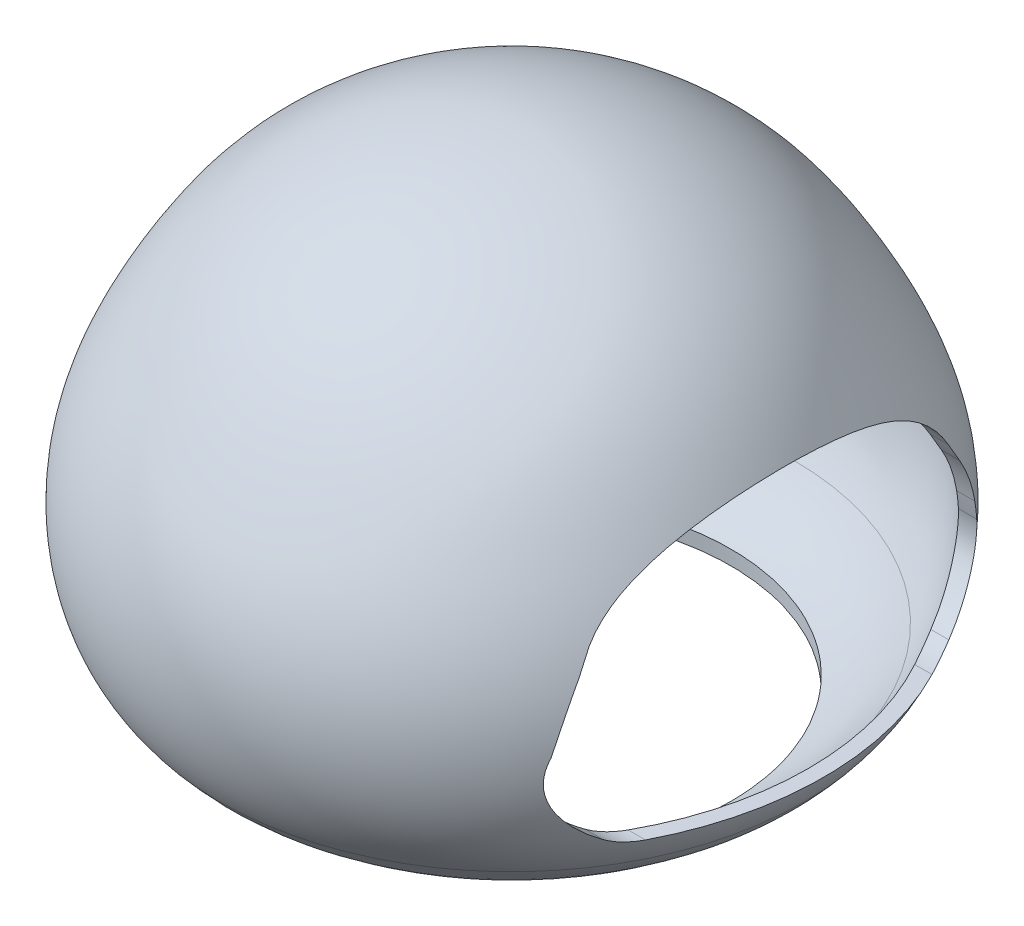
SolidWorks part; units mm, degrees
ref_plane "Front Plane" through (0, 0, 0) normal (0, 0, 1) x (1, 0, 0)
ref_plane "Top Plane" through (0, 0, 0) normal (0, 1, 0) x (1, 0, 0)
ref_plane "Right Plane" through (0, 0, 0) normal (1, 0, 0) x (0, 0, -1)
sketch "Sketch3" plane through (0, 0, 0) normal (0, 0, 1) x (1, 0, 0)
  line L0 (0.0245, 157.0849) -> (0.0245, 152.0849)
  line L1 (0.0245, -20.9434) -> (0.0245, -25.9434)
  line L2 (0.0245, 171.6103) -> (0.0245, -40.6784) construction
  spline S0 degree 3 poles (-103.1746, 0) (-78.8328, -30.0641) (-33.4587, -20.9434) (0.0245, -20.9434) knots 0 0 0 0 1 1 1 1
  spline S1 degree 3 poles (-103.1746, 0) (-114.7602, 14.5762) (-119.8367, 49.2728) (-101.4518, 88.6739) (-71.3798, 134.4794) (-29.75, 152.0849) (0.0245, 152.0849) knots 0 0 0 0 0.250738 0.442513 0.587645 1 1 1 1
  spline S2 degree 1 poles (-107.0747, -3.1288) (0.0245, -25.9434) knots 0 0 1 1 construction
  spline S3 degree 1 poles (-107.0747, -3.1288) (0.0245, 157.0849) knots 0 0 1 1 construction
  spline S4 degree 3 poles (0.0245, -25.9434) (-1.0078, -25.9434) (-3.0527, -25.9607) (-7.3007, -26.054) (-12.7748, -26.2598) (-19.5869, -26.581) (-28.9113, -27.0143) (-40.9004, -27.387) (-55.4438, -26.9753) (-69.7899, -25.0863) (-81.2787, -21.7225) (-89.9598, -17.6028) (-96.1383, -13.7178) (-100.9459, -9.7522) (-104.5344, -6.1303) (-106.2545, -4.1419) (-107.0747, -3.1288) knots -0.000194 -0.000194 -0.000194 -0.000194 0.031062 0.062318 0.12483 0.187342 0.249854 0.374879 0.499903 0.624927 0.749951 0.812464 0.874976 0.937488 0.968744 1 1 1 1
  spline S5 degree 3 poles (-107.0747, -3.1288) (-107.8617, -2.1388) (-109.3756, -0.1005) (-112.0955, 4.1156) (-114.956, 9.6441) (-117.5537, 16.5853) (-119.9627, 26.1346) (-121.1031, 38.4065) (-119.7936, 53.0884) (-116.0899, 67.0475) (-110.6339, 80.233) (-104.0343, 92.719) (-96.8153, 104.7516) (-88.5122, 116.2468) (-78.6677, 126.6978) (-67.4647, 135.7136) (-55.1826, 143.2806) (-42.0542, 149.311) (-28.3211, 153.7314) (-14.2042, 156.4574) (-4.7225, 157.0849) (0.0245, 157.0849) knots -0.000101 -0.000101 -0.000101 -0.000101 0.015525 0.031152 0.062405 0.093658 0.124911 0.187418 0.249924 0.31243 0.374937 0.437443 0.499949 0.562456 0.624962 0.687468 0.749975 0.812481 0.874987 0.937494 1 1 1 1
  dimension "D1" = 5
revolve "Revolve5" add sketch "Sketch3" angle 360 about L2
ref_plane "Plane2" through (0, -30, 0) normal (0, 1, 0) x (1, 0, 0)
sketch "Sketch4" plane through (0, -30, 0) normal (0, 1, 0) x (1, 0, 0)
  circle A0 centre (0, 0) radius 80.1001
extrude "Cut-Extrude2" cut sketch "Sketch4" along normal blind 20
sketch "Sketch5" plane through (0, 0, 0) normal (1, 0, 0) x (0, 0, -1)
  line L0 (-52.4765, 8.1366) -> (52.4765, 8.1366)
  arc A0 (-52.4765, 8.1366) -> (-63.3365, 11.3419) centre (-52.4765, 28.1366) cw
  arc A1 (52.4765, 8.1366) -> (63.3365, 11.3419) centre (52.4765, 28.1366) ccw
  arc A2 (-69.3418, 64.1464) -> (-67.0221, 68.7237) centre (-184.1186, 125.1898) ccw
  arc A3 (70.4941, 63.0471) -> (66.203, 70.3101) centre (188.8284, 137.8602) cw
  arc A4 (78.7462, 39.318) -> (77.2009, 46.2401) centre (214.5664, 73.272) cw
  ellipse E0 centre (0, 56.3684) end of major axis (69.9377, 56.3684) minor radius 43.2422 (66.203, 70.3101) -> (-67.0221, 68.7237) ccw
  ellipse E1 centre (0, 34.6362) end of major axis (79.3292, 34.6362) minor radius 38.6866 (-77.8366, 42.1057) -> (-63.3365, 11.3419) ccw
  ellipse E2 centre (0, 34.6362) end of major axis (79.3292, 34.6362) minor radius 38.6866 (63.3365, 11.3419) -> (78.7462, 39.318) ccw
  spline S0 degree 3 poles (-69.3418, 64.1464) (-73.0617, 57.1522) (-75.8989, 49.7908) (-77.8366, 42.1057) knots 0.114274 0.114274 0.114274 0.114274 1 1 1 1
  spline S1 degree 3 poles (70.4941, 63.0471) (72.3563, 60.1016) (75.0451, 54.6733) (76.6927, 48.8224) (77.2009, 46.2401) knots 0.168182 0.168182 0.168182 0.168182 0.552819 0.845618 0.845618 0.845618 0.845618
  dimension "D1" = 20
  dimension "D2" = 130
  dimension "D3" = 140
  dimension "D4" = 140
extrude "Cut-Extrude3" cut sketch "Sketch5" along normal through all
scale "Scale2" bodies to scale 106 scale about centroid uniform scaling yes scale factor 1
ref_plane "Plane3" through (0, 105, 0) normal (0, 1, 0) x (1, 0, 0)
sketch "Sketch6" plane through (0, 105, 0) normal (0, 1, 0) x (1, 0, 0)
  circle A0 centre (0, 0) radius 10
extrude "Boss-Extrude1" add sketch "Sketch6" against normal up to surface (46.603 mm away)
